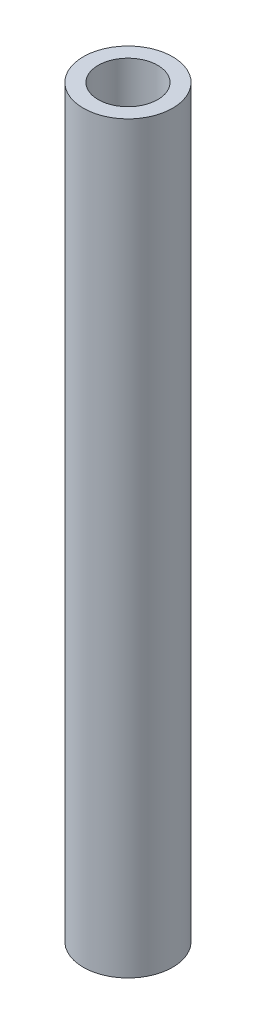
SolidWorks part; units mm, degrees
ref_plane "Front Plane" through (0, 0, 0) normal (0, 0, 1) x (1, 0, 0)
ref_plane "Top Plane" through (0, 0, 0) normal (0, 1, 0) x (1, 0, 0)
ref_plane "Right Plane" through (0, 0, 0) normal (1, 0, 0) x (0, 0, -1)
sketch "Sketch1" plane through (0, 0, 0) normal (0, 1, 0) x (1, 0, 0)
  circle A0 centre (0, 0) radius 3
  circle A1 centre (0, 0) radius 2
  dimension "D1" = 6
  dimension "D2" = 4
extrude "Boss-Extrude1" add sketch "Sketch1" along normal blind 50
